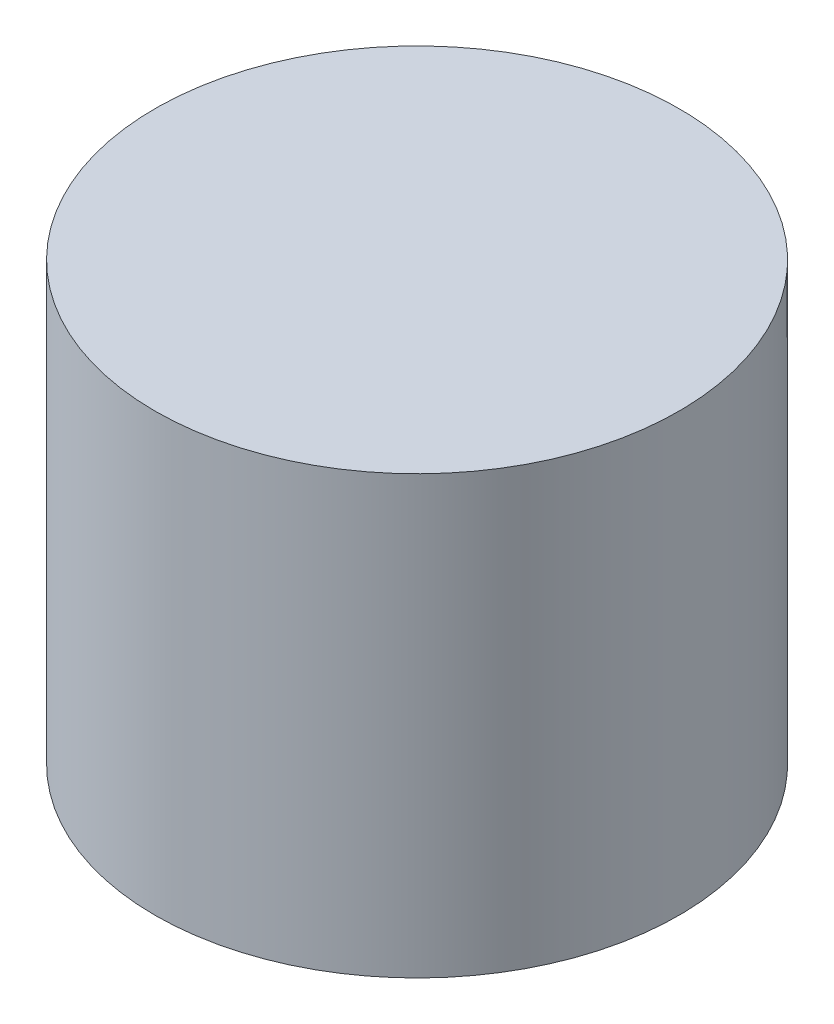
SolidWorks part; units mm, degrees
ref_plane "Front Plane" through (0, 0, 0) normal (0, 0, 1) x (1, 0, 0)
ref_plane "Top Plane" through (0, 0, 0) normal (0, 1, 0) x (1, 0, 0)
ref_plane "Right Plane" through (0, 0, 0) normal (1, 0, 0) x (0, 0, -1)
sketch "Sketch1" plane through (0, 0, 0) normal (0, 1, 0) x (1, 0, 0)
  circle A0 centre (0, 0) radius 7.5
  point P2 (0, 0)
  dimension "D1" = 15
extrude "Boss-Extrude1" add sketch "Sketch1" along normal blind 12.5
